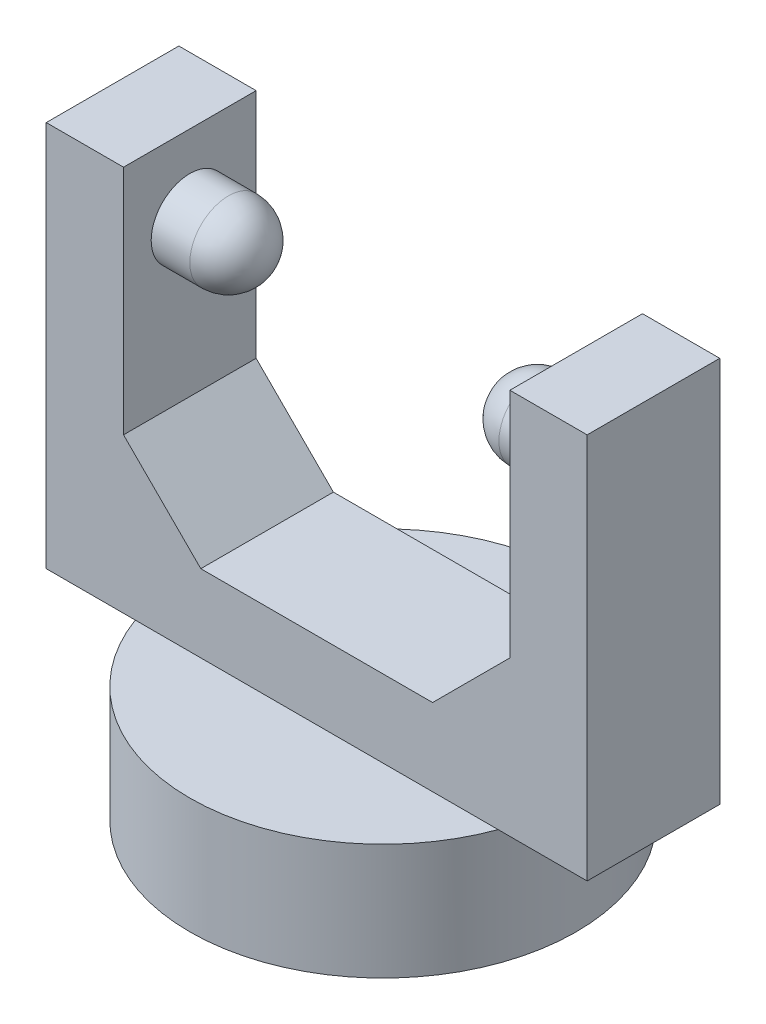
SolidWorks part; units mm, degrees
ref_plane "Front Plane" through (0, 0, 0) normal (0, 0, 1) x (1, 0, 0)
ref_plane "Top Plane" through (0, 0, 0) normal (0, 1, 0) x (1, 0, 0)
ref_plane "Right Plane" through (0, 0, 0) normal (1, 0, 0) x (0, 0, -1)
sketch "Sketch1" plane through (0, 0, 0) normal (0, 1, 0) x (1, 0, 0)
  circle A0 centre (0, 0) radius 12.5
  dimension "D1" = 25
extrude "Boss-Extrude1" add sketch "Sketch1" along normal blind 7.5
sketch "Sketch2" plane through (0, 7.5, 0) normal (0, 1, 0) x (1, 0, 0)
  line L1 (-17.5, 4.2904) -> (17.5, 4.2904)
  line L2 (-17.5, 4.2904) -> (-17.5, -4.2904)
  line L3 (-17.5, -4.2904) -> (17.5, -4.2904)
  line L4 (17.5, 4.2904) -> (17.5, -4.2904)
  point P4 (17.5, 0)
  point P6 (0, 4.2904)
  dimension "D1" = 35
  dimension "D3" = 8.5808
extrude "Boss-Extrude2" add sketch "Sketch2" along normal blind 25
sketch "Sketch3" plane through (0, 32.5, 0) normal (0, 1, 0) x (1, 0, 0)
  line L0 (17.5, 4.2904) -> (-17.5, 4.2904) construction
  line L1 (-12.5, 4.2904) -> (12.5, 4.2904)
  line L2 (-12.5, 4.2904) -> (-12.5, -4.2904)
  line L3 (-12.5, -4.2904) -> (12.5, -4.2904)
  line L4 (12.5, 4.2904) -> (12.5, -4.2904)
  line L5 (-17.5, -4.2904) -> (17.5, -4.2904) construction
  line L6 (17.5, -4.2904) -> (17.5, 4.2904) construction
  line L7 (-17.5, 4.2904) -> (-17.5, -4.2904) construction
  dimension "D1" = 5
  dimension "D2" = 5
extrude "Cut-Extrude1" cut sketch "Sketch3" against normal blind 20
sketch "Sketch4" plane through (-12.5, 0, 0) normal (1, 0, 0) x (0, 0, -1)
  line L0 (4.2904, 12.5) -> (-4.2904, 12.5) construction
  line L1 (4.2904, 32.5) -> (-4.2904, 32.5) construction
  circle A0 centre (0, 27.5) radius 2.5
  point P8 (0, 32.5)
  dimension "D1" = 5
  dimension "D2" = 15
extrude "Boss-Extrude3" add sketch "Sketch4" along normal blind 5
sketch "Sketch5" plane through (12.5, 0, 0) normal (-1, 0, 0) x (0, 0, 1)
  circle A0 centre (0, 27.5) radius 2.5
  circle A1 centre (0, 27.5) radius 2.5 construction
  dimension "D1" = 5
extrude "Boss-Extrude4" add sketch "Sketch5" along normal blind 5
chamfer "Chamfer1" distance 5 angle 45 1 edges at (-12.5, 12.5, 0)
chamfer "Chamfer2" distance 5 angle 45 1 edges at (12.5, 12.5, 0)
fillet "Fillet1" radius 2.5 1 edges at (-7.5, 27.5, -2.5)
fillet "Fillet2" radius 2.5 1 edges at (7.5, 27.5, 2.5)
